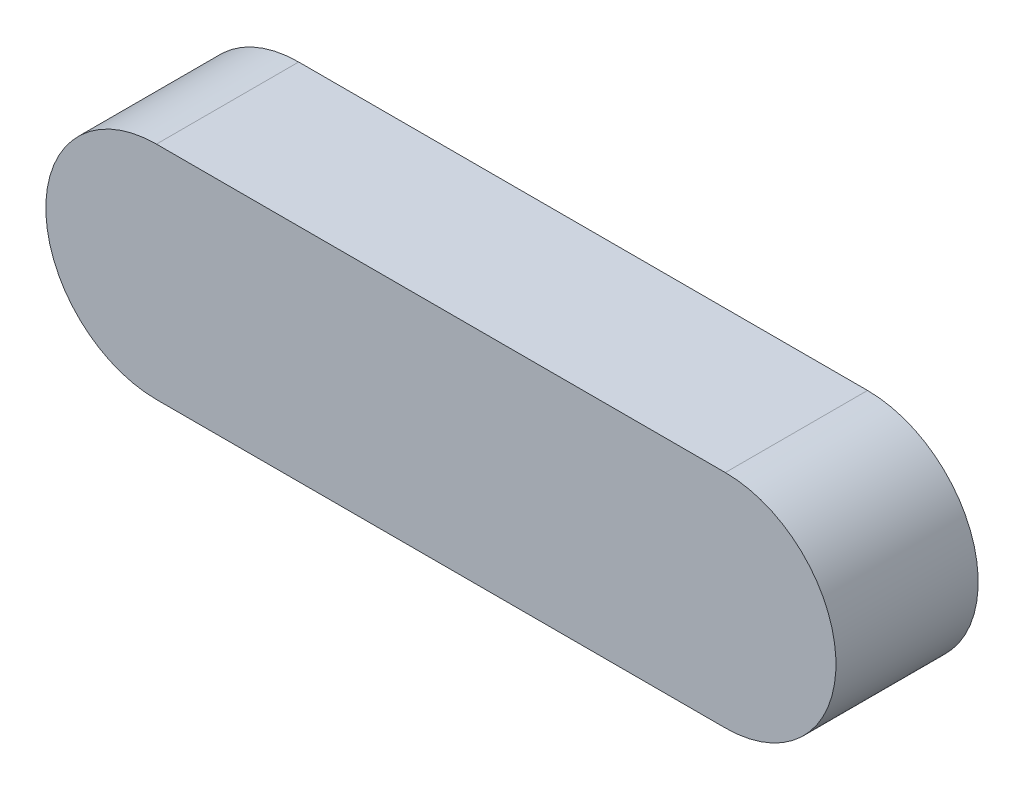
SolidWorks part; units mm, degrees
ref_plane "Front Plane" through (0, 0, 0) normal (0, 0, 1) x (1, 0, 0)
ref_plane "Top Plane" through (0, 0, 0) normal (0, 1, 0) x (1, 0, 0)
ref_plane "Right Plane" through (0, 0, 0) normal (1, 0, 0) x (0, 0, -1)
sketch "Sketch1" plane through (0, 0, 0) normal (0, 0, 1) x (1, 0, 0)
  line L0 (0, 0) -> (36, 0) construction
  line L1 (0, 7) -> (36, 7)
  line L2 (0, -7) -> (36, -7)
  arc A0 (0, 7) -> (0, -7) centre (0, 0) ccw
  arc A1 (36, -7) -> (36, 7) centre (36, 0) ccw
  point P3 (18, 0)
  dimension "D2" = 7
  dimension "D1" = 36
extrude "Boss-Extrude1" add sketch "Sketch1" along normal blind 9
